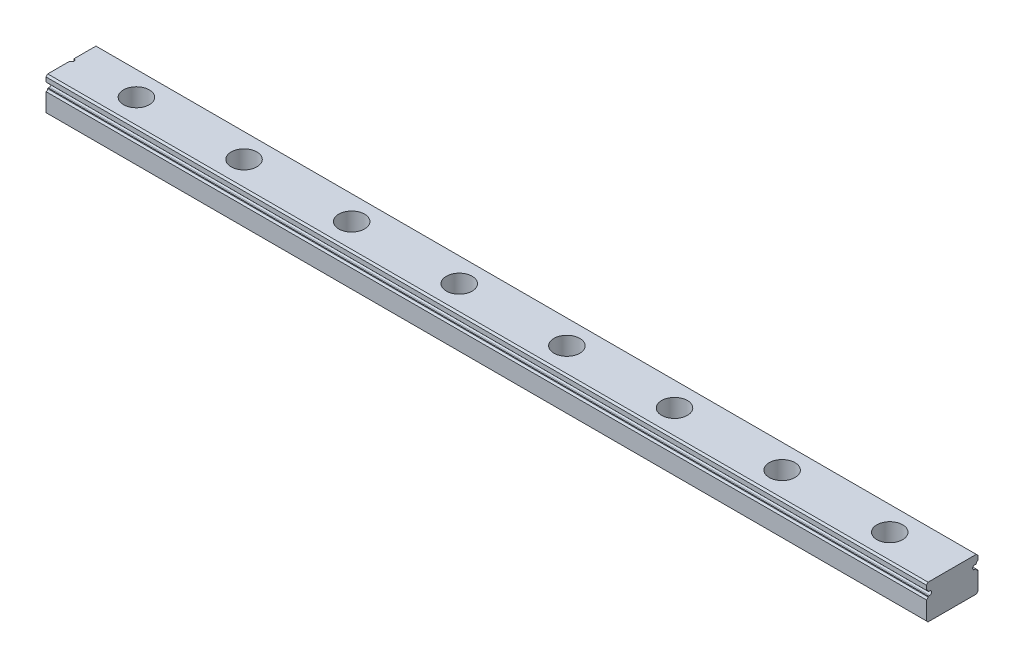
SolidWorks part; units mm, degrees
material "Chrome Stainless Steel"
ref_plane "Front Plane" through (0, 0, 0) normal (0, 0, 1) x (1, 0, 0)
ref_plane "Top Plane" through (0, 0, 0) normal (0, 1, 0) x (1, 0, 0)
ref_plane "Right Plane" through (0, 0, 0) normal (1, 0, 0) x (0, 0, -1)
sketch "Sketch1" plane through (0, 0, 0) normal (1, 0, 0) x (0, 0, -1)
  line L0 (3, 1.6) -> (0.6714, 1.6) construction
  line L1 (-3, -4) -> (2.6, -4)
  line L2 (-3, -4) -> (-3, 4)
  line L3 (-3, 4) -> (2.6, 4)
  line L4 (3, -3.6) -> (3, 0.64)
  line L5 (-3, -4) -> (3, 4) construction
  line L6 (-3, 4) -> (3, -4) construction
  line L7 (2.2, 2.05) -> (2.5, 2.05)
  line L8 (2.6, 1.04) -> (2.5, 1.15)
  line L9 (3, 2.16) -> (2.4728, 2.16) construction
  line L10 (2.6, 2.16) -> (2.5, 2.05)
  line L11 (2.2, 1.15) -> (2.5, 1.15)
  line L12 (3, 2.56) -> (3, 3.6)
  line L13 (2.6, 4) -> (3, 3.6)
  line L14 (2.6, -4) -> (3, -3.6)
  arc A0 (2.2, 2.05) -> (2.2, 1.15) centre (2.2, 1.6) ccw
  arc A1 (3, 2.56) -> (2.6, 2.16) centre (3, 2.16) ccw
  arc A2 (3, 0.64) -> (2.6, 1.04) centre (3, 1.04) cw
  point P0 (0, 0)
  dimension "D4" = 0.8
  dimension "D5" = 0.9
  dimension "D6" = 0.56
  dimension "D7" = 0.8
  dimension "D8" = 0
  dimension "D9" = 0.5
  dimension "D1" = 6
  dimension "D2" = 8
  dimension "D3" = 2.4
extrude "Boss-Extrude1" add sketch "Sketch1" along normal blind 480
mirror "Mirror1" about plane through (480, -4, 3) normal (0, 0, -1) of "Boss-Extrude1"
sketch "Sketch2" plane through (0, 4, 0) normal (0, 1, 0) x (1, 0, 0)
  line L0 (480, -3) -> (-450, -3) construction
  line L1 (480, 2.6) -> (480, -8.6) construction
  line L2 (0, 2.6) -> (0, -8.6) construction
  circle A0 centre (15, -3) radius 1.75
  dimension "D1" = 3.5
  dimension "D2" = 15
extrude "Cut-Extrude1" cut sketch "Sketch2" against normal blind 60
sketch "Sketch3" plane through (0, 4, 0) normal (0, 1, 0) x (1, 0, 0)
  circle A0 centre (15, -3) radius 3
  dimension "D1" = 6
extrude "Cut-Extrude2" cut sketch "Sketch3" against normal blind 4.5
sketch "Sketch4" plane through (0, 4, 0) normal (0, 1, 0) x (1, 0, 0)
  line L0 (0, 2.6) -> (0, -8.6) construction
  circle A0 centre (0, -3) radius 0.5
  dimension "D1" = 1
extrude "Cut-Extrude3" cut sketch "Sketch4" against normal blind 14.5
pattern_linear "LPattern1" count 19 spacing 25 along (1, 0, 0) of "Cut-Extrude2", "Cut-Extrude1"
sketch "Sketch5" plane through (0, -4, 0) normal (0, -1, 0) x (1, 0, 0)
  line L1 (0, -3) -> (204.5, -3) construction
  line L2 (0, -3) -> (0, 40.065) construction
  line L3 (0, 40.065) -> (204.5, 40.065) construction
  line L4 (204.5, -3) -> (204.5, 40.065) construction
  line L5 (204.5, -3) -> (511.9736, -3)
  line L6 (204.5, -3) -> (204.5, 29.3616)
  line L7 (204.5, 29.3616) -> (511.9736, 29.3616)
  line L8 (511.9736, -3) -> (511.9736, 29.3616)
  dimension "D1" = 204.5
extrude "Cut-Extrude4" cut sketch "Sketch5" against normal through all
equation "\"print_x\"= 374"
equation "\"print_y\"= 250"
equation "\"XYB_margin_left\"= 81"
equation "\"XYB_margin_right\"= 95"
equation "\"XYB_margin_front\"= 59"
equation "\"XYB_margin_back\"= 112"
equation "\"XYB_border_left\"= 47"
equation "\"XYB_border_right\"= 47"
equation "\"XYB_border_front\"= 32"
equation "\"XYB_border_back\"= 80"
equation "\"XYB_total_x\"= 550"
equation "\"XYB_total_y\"= 421"
equation "\"XYB_morot_slot\"= 3"
equation "\"XYB_ful_x\"= 5.6"
equation "\"XYB_ful_y\"= 12"
equation "\"XYB_ful_tav\"= 434"
equation "\"XYB_ful_offset_y\"= 18"
equation "\"XYB_ful_offset_x\"= 20"
equation "\"XYB_sin_x\"= 14"
equation "\"XYB_sin_y\"= 55"
equation "\"XYB_sin_furat\"= 4.21"
equation "\"XYB_sin_furatszam\"= 6"
equation "\"XYB_sin_furat_offset\"= 50"
equation "\"MNG_Y_len\"= 310"
equation "\"D1@Boss-Extrude1\"=\"MNG_X_len\""
equation "\"XYB_motor_x\"= 39"
equation "\"XYB_hezag\"= 2"
equation "\"MNG_X_len\"= 430"
equation "\"XCROSS_luktav\"= 20"
equation "\"XCROSS_len\"= 549"
equation "\"midful_hasitas\"= 180"
equation "\"xsinpemfuratok\"= 16"
equation "\"print_z\"= 250"
equation "\"XYB_szij\"= 52.5"
equation "\"zmove\"= 255"
equation "\"BS_also_holtter\"= 100"
equation "\"BS_felso_holtter\"= 25"
equation "\"BS_len\"= 380"
equation "\"mng_x_firstoffset\"= 15"
equation "\"D2@Sketch2\"=\"mng_x_firstoffset\""
